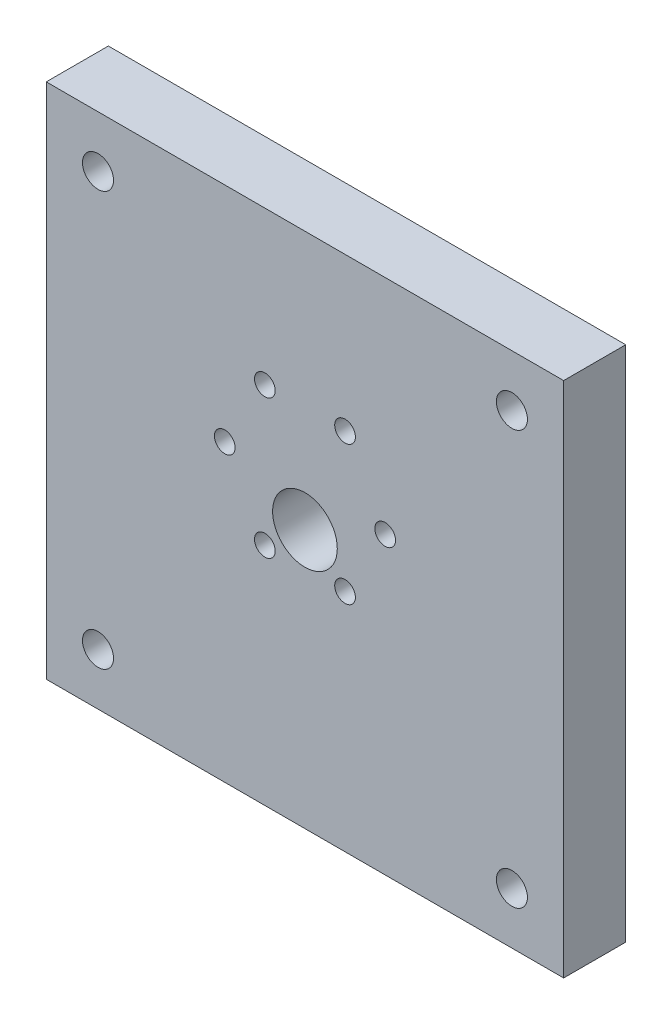
SolidWorks part; units mm, degrees
ref_plane "Plan de face" through (0, 0, 0) normal (0, 0, 1) x (1, 0, 0)
ref_plane "Plan de dessus" through (0, 0, 0) normal (0, 1, 0) x (1, 0, 0)
ref_plane "Plan de droite" through (0, 0, 0) normal (1, 0, 0) x (0, 0, -1)
sketch "Esquisse1" plane through (0, 0, 0) normal (0, 0, 1) x (1, 0, 0)
  circle A0 centre (0, 0) radius 18.5
  dimension "D1" = 37
extrude "Boss.-Extru.1" add sketch "Esquisse1" along normal blind 12
sketch "Esquisse2" plane through (0, 0, 12) normal (0, 0, 1) x (1, 0, 0)
  line L0 (-18.5, 0) -> (18.5, 0) construction
  circle A0 centre (0, 0) radius 18.5 construction
  circle A1 centre (-15.5, 0) radius 2
  circle A2 centre (15.5, 0) radius 2
  circle A3 centre (7.75, -13.4234) radius 2
  circle A4 centre (-7.75, -13.4234) radius 2
  circle A5 centre (-15.5, 0) radius 2
  circle A6 centre (-7.75, 13.4234) radius 2
  circle A7 centre (7.75, 13.4234) radius 2
  point P22 (0, 0)
  dimension "D1" = 31
  dimension "D2" = 15.5
  dimension "D3" = 4
  dimension "D4" = 4
  dimension "D5" = 6
extrude "Enlèv. mat.-Extru.1" cut sketch "Esquisse2" against normal through all contours A6 | A7 | A2 L0 | L0 A2 | A3 | A4 | L0 A5 | A1 L0
sketch "Esquisse3" plane through (0, 0, 12) normal (0, 0, 1) x (1, 0, 0)
  circle A0 centre (0, -7) radius 6.25
  dimension "D1" = 12.5
  dimension "D3" = 7
extrude "Enlèv. mat.-Extru.2" cut sketch "Esquisse3" against normal through all
sketch "Esquisse4" plane through (0, 0, 12) normal (0, 0, 1) x (1, 0, 0)
  line L1 (50, 43) -> (-50, 43)
  line L2 (50, 43) -> (50, -57)
  line L3 (50, -57) -> (-50, -57)
  line L4 (-50, 43) -> (-50, -57)
  line L5 (50, 43) -> (-50, -57) construction
  line L6 (50, -57) -> (-50, 43) construction
  circle A0 centre (0, 0) radius 18.5
  point P3 (0, -7)
  dimension "D1" = 100
  dimension "D2" = 100
extrude "Boss.-Extru.2" add sketch "Esquisse4" against normal blind 12 contours L2 L1 L4 L3 | A0
sketch "Esquisse5" plane through (0, 0, 12) normal (0, 0, 1) x (1, 0, 0)
  line L0 (50, 43) -> (-50, 43) construction
  line L1 (-50, 43) -> (-50, -57) construction
  circle A0 centre (-40, 33) radius 3
  circle A1 centre (40, 33) radius 3
  circle A2 centre (40, -47) radius 3
  circle A3 centre (-40, -47) radius 3
  dimension "D1" = 6
  dimension "D2" = 10
  dimension "D3" = 10
  dimension "D4" = 2
  dimension "D5" = 2
extrude "Enlèv. mat.-Extru.3" cut sketch "Esquisse5" against normal blind 12
